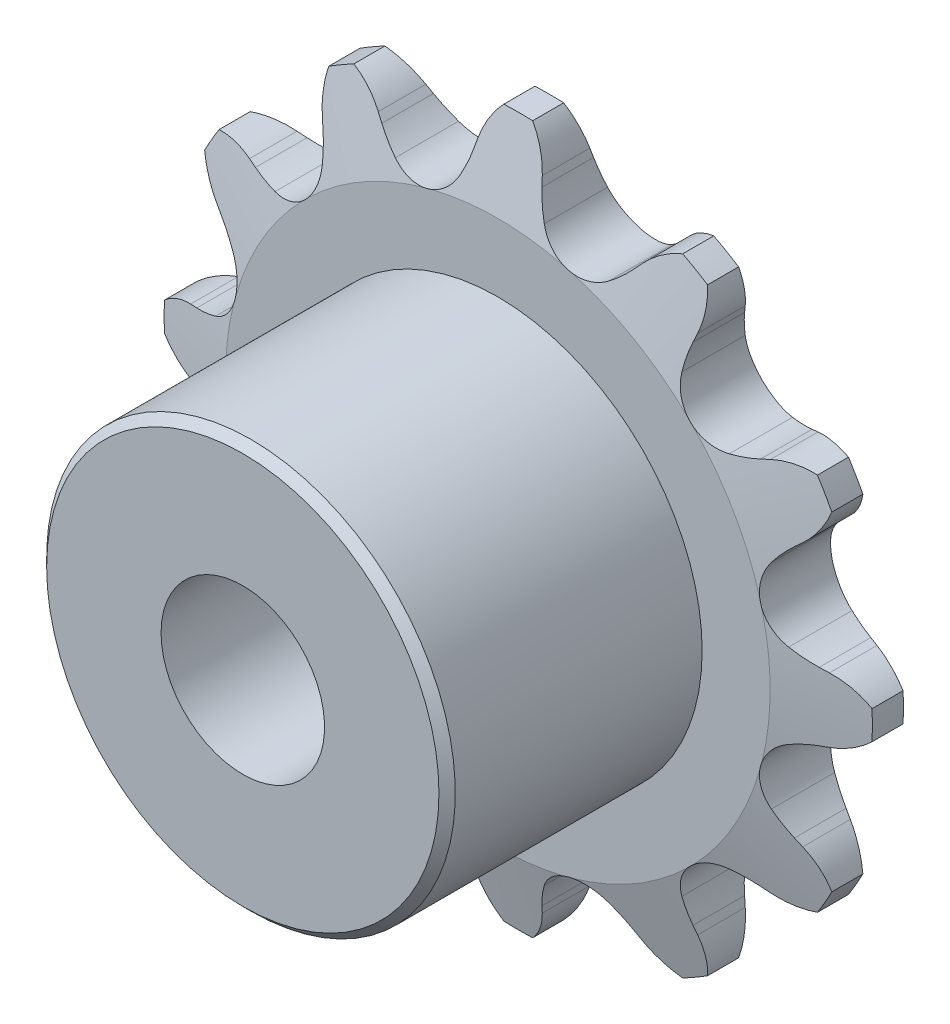
SolidWorks part; units mm, degrees
ref_plane "Front Plane" through (0, 0, 0) normal (0, 0, 1) x (1, 0, 0)
ref_plane "Top Plane" through (0, 0, 0) normal (0, 1, 0) x (1, 0, 0)
ref_plane "Right Plane" through (0, 0, 0) normal (1, 0, 0) x (0, 0, -1)
sketch "Sketch0" plane through (0, 0, 0) normal (0, 0, 1) x (1, 0, 0)
  line L0 (3.175, -11.8493) -> (0, 0) construction
  line L1 (0, 0) -> (8.6743, -8.6743) construction
  line L2 (0, 0) -> (-3.175, -11.8493) construction
  line L3 (3.175, -11.8493) -> (8.6743, -8.6743) construction
  line L4 (3.175, -11.8493) -> (-3.175, -11.8493) construction
  line L5 (5.1176, -11.3719) -> (4.9011, -11.1286)
  line L6 (3.175, -11.8493) -> (0, -12.7) construction
  line L7 (1.2539, -12.4071) -> (1.3198, -12.0882)
  line L8 (0, -11.8493) -> (0, -13.7543) construction
  line L9 (4.1486, -10.4589) -> (1.6598, -14.0131) construction
  line L10 (0, 0) -> (0, -11.8493) construction
  line L11 (4.9011, -11.1286) -> (1.6598, -14.0131) construction
  line L12 (0, -13.7543) -> (0, -14.1976) construction
  line L13 (7.1785, -9.5379) -> (5.1176, -11.3719) construction
  circle A0 centre (0, 0) radius 13.7543 construction
  circle A1 centre (0, 0) radius 12.2673 construction
  arc A2 (-1.7824, -14.5876) -> (8.8374, -11.7421) centre (0, 0) ccw
  circle A3 centre (0, 0) radius 14.1976 construction
  circle A4 centre (3.175, -11.8493) radius 1.651 construction
  arc A7 (4.1486, -10.4589) -> (1.6367, -11.1319) centre (3.175, -11.8493) ccw
  circle A8 centre (3.175, -11.8493) radius 1.6974 construction
  arc A9 (5.1176, -11.3719) -> (8.8374, -11.7421) centre (7.1785, -9.5379) ccw
  arc A10 (4.9011, -11.1286) -> (4.1486, -10.4589) centre (1.6598, -14.0131) ccw
  arc A11 (1.2539, -12.4071) -> (-1.7824, -14.5876) centre (-1.4478, -11.8493) cw
  arc A12 (1.3198, -12.0882) -> (1.6367, -11.1319) centre (5.5691, -12.9656) cw
  dimension "D1" = 1.6974
  dimension "R" = 1.6974
sketch "Sketch1" plane through (0, 0, 0) normal (1, 0, 0) x (0, 0, -1)
  line L0 (1.397, 0) -> (-1.397, 0)
  line L1 (-1.397, 0) -> (-1.397, 10.5793)
  line L2 (-1.397, 10.5793) -> (-0.6033, 13.7543)
  line L3 (-0.6033, 13.7543) -> (0.6033, 13.7543)
  line L4 (0.6033, 13.7543) -> (1.397, 10.5793)
  line L5 (1.397, 10.5793) -> (1.397, 0)
  line L7 (0, 13.7543) -> (0, 0) construction
  line L8 (-1.397, 10.5793) -> (1.397, 10.5793) construction
  line L9 (0, 13.7543) -> (0, -13.7543) construction
  line L10 (-1.397, 10.5793) -> (-1.397, 13.7543) construction
  line L11 (-1.397, 13.7543) -> (-0.6033, 13.7543) construction
  line L12 (0.6033, 13.7543) -> (1.397, 13.7543) construction
  line L13 (1.397, 13.7543) -> (1.397, 10.5793) construction
  line L14 (0, 0) -> (-6.4008, 0) construction
  line L22 (1.397, 0) -> (-11.303, 0) construction
  line L24 (-1.397, 0) -> (-1.397, 8.2933) construction
revolve "Revolve1" add sketch "Sketch1" angle 360 mid plane about L0
extrude "Cut-Extrude1" cut sketch "Sketch0" against normal through all and the other way through all
pattern_circular "CirPattern1" count 12 over 360 about axis through (0, 0, 0) along (0, 0, 1) of "Cut-Extrude1"
sketch "Sketch2" plane through (0, 0, 0) normal (0, 0, 1) x (1, 0, 0)
  circle A0 centre (0, 0) radius 3.175 construction
  circle A1 centre (0, 0) radius 7.9375
  circle A2 centre (0, 0) radius 13.716 construction
  dimension "Bore" = 6.35
  dimension "Hub Dia." = 15.875
  dimension "OD" = 27.432
extrude "Boss-Extrude1" add sketch "Sketch2" along normal up to vertex (11.303 mm away) from surface at 1.397 starting at face at (0, 0, 1.397)
sketch "Sketch3" plane through (0, 0, 0) normal (0, 0, 1) x (1, 0, 0)
  circle A0 centre (0, 0) radius 3.175 construction
  circle A1 centre (0, 0) radius 3.175
extrude "Cut-Extrude2" cut sketch "Sketch3" along normal through all and the other way through all
sketch "Sketch4" plane through (0, 0, 0) normal (1, 0, 0) x (0, 0, -1)
  line L0 (-11.303, 7.9375) -> (-11.303, 7.62)
  line L1 (-1.397, 13.7543) -> (-3.4925, 13.7543)
  line L2 (-1.397, 13.7543) -> (-1.397, 8.2933)
  line L3 (-1.397, 8.2933) -> (-3.4925, 8.2933)
  line L4 (-3.4925, 13.7543) -> (-3.4925, 8.2933)
  line L9 (-11.303, 7.62) -> (-10.9855, 7.9375)
  line L10 (-10.9855, 7.9375) -> (-11.303, 7.9375)
  dimension "C" = 0.3175
  dimension "D3" = 2.0955
revolve "Cut-Revolve1" cut sketch "Sketch4" angle 360 mid plane about L22
equation "\"360/N@Sketch0\" = 360/\"Teeth@CirPattern1\""
equation "\"Ds@Sketch0\" = 1.005 * \"Dr@Sketch0\" + 0.003"
equation "\"R@Sketch0\" = 1/2 * \"Ds@Sketch0\""
equation "\"A@Sketch0\" = 35 +  ( 60 / \"Teeth@CirPattern1\" ) "
equation "\"B@Sketch0\" = 18 -  ( 56 / \"Teeth@CirPattern1\" )"
equation "\"ac@Sketch0\" = 0.8 * \"Dr@Sketch0\""
equation "\"ab@Sketch0\" = 1.4 * \"Dr@Sketch0\""
equation "\"J@Sketch0\" = 0.3 * \"Pitch@Sketch0\""
equation "\"h@Sketch1\" = \"Pitch@Sketch0\" / 2"
equation "\"g@Sketch1\" = \"h@Sketch1\" / 4"
equation "\"MHD@Sketch1\" = \"Pitch@Sketch0\" * ( cotan ( 180 / \"Teeth@CirPattern1\" ) - 1 ) - 0.030"
equation "\"D3@Sketch4\" = \"t@Sketch1\" * 3 / 4"
